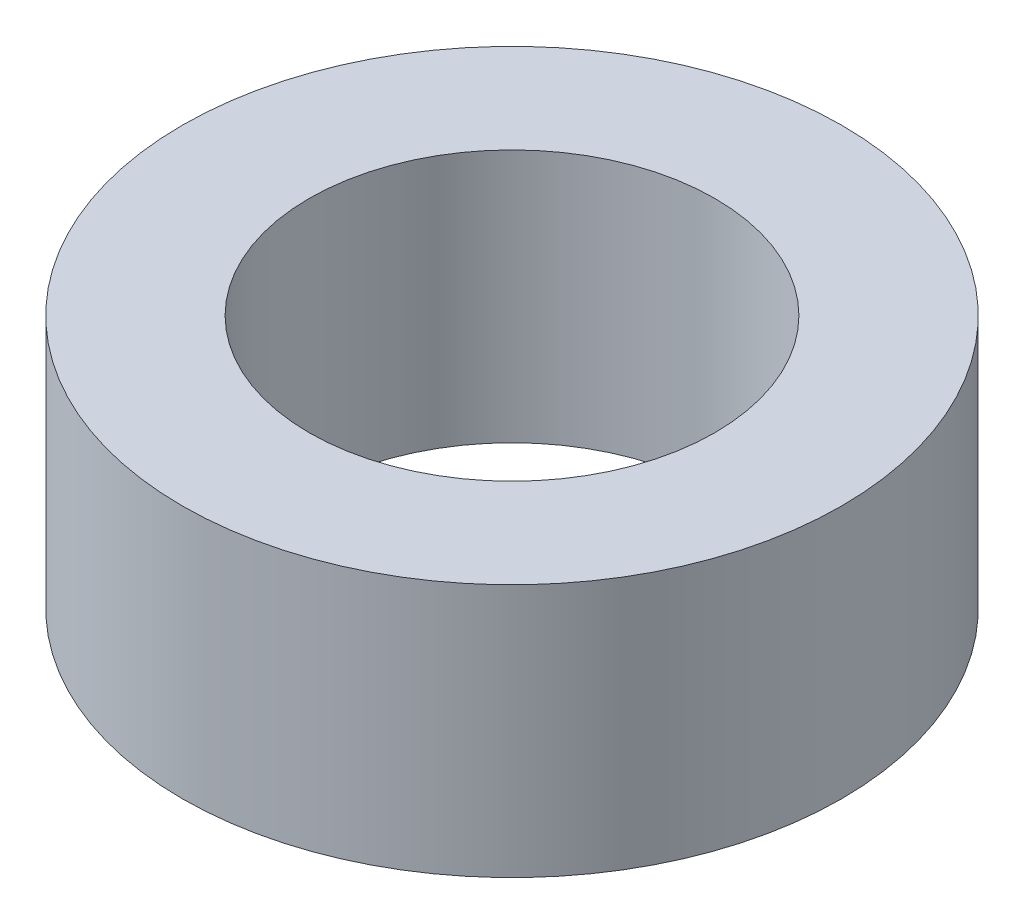
SolidWorks part; units mm, degrees
ref_plane "Front Plane" through (0, 0, 0) normal (0, 0, 1) x (1, 0, 0)
ref_plane "Top Plane" through (0, 0, 0) normal (0, 1, 0) x (1, 0, 0)
ref_plane "Right Plane" through (0, 0, 0) normal (1, 0, 0) x (0, 0, -1)
sketch "Sketch2" plane through (0, 0, 0) normal (0, 1, 0) x (1, 0, 0)
  circle A0 centre (0, 0) radius 3.2
  circle A1 centre (0, 0) radius 5.2
  dimension "D1" = 6.4
  dimension "D2" = 2
extrude "Boss-Extrude1" add sketch "Sketch2" along normal blind 4
